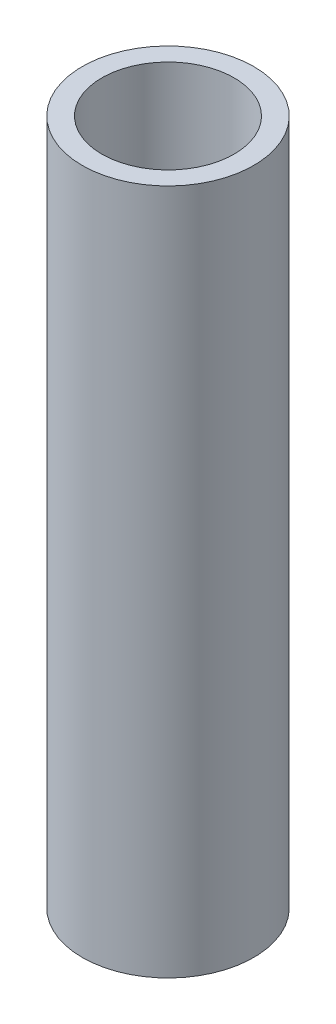
SolidWorks part; units mm, degrees
ref_plane "Front Plane" through (0, 0, 0) normal (0, 0, 1) x (1, 0, 0)
ref_plane "Top Plane" through (0, 0, 0) normal (0, 1, 0) x (1, 0, 0)
ref_plane "Right Plane" through (0, 0, 0) normal (1, 0, 0) x (0, 0, -1)
sketch "Sketch1" plane through (0, 0, 0) normal (0, 1, 0) x (1, 0, 0)
  circle A0 centre (0, 0) radius 6.75
  circle A1 centre (0, 0) radius 8.75
  dimension "D1" = 13.5
  dimension "D2" = 2
extrude "Boss-Extrude1" add sketch "Sketch1" along normal blind 70
